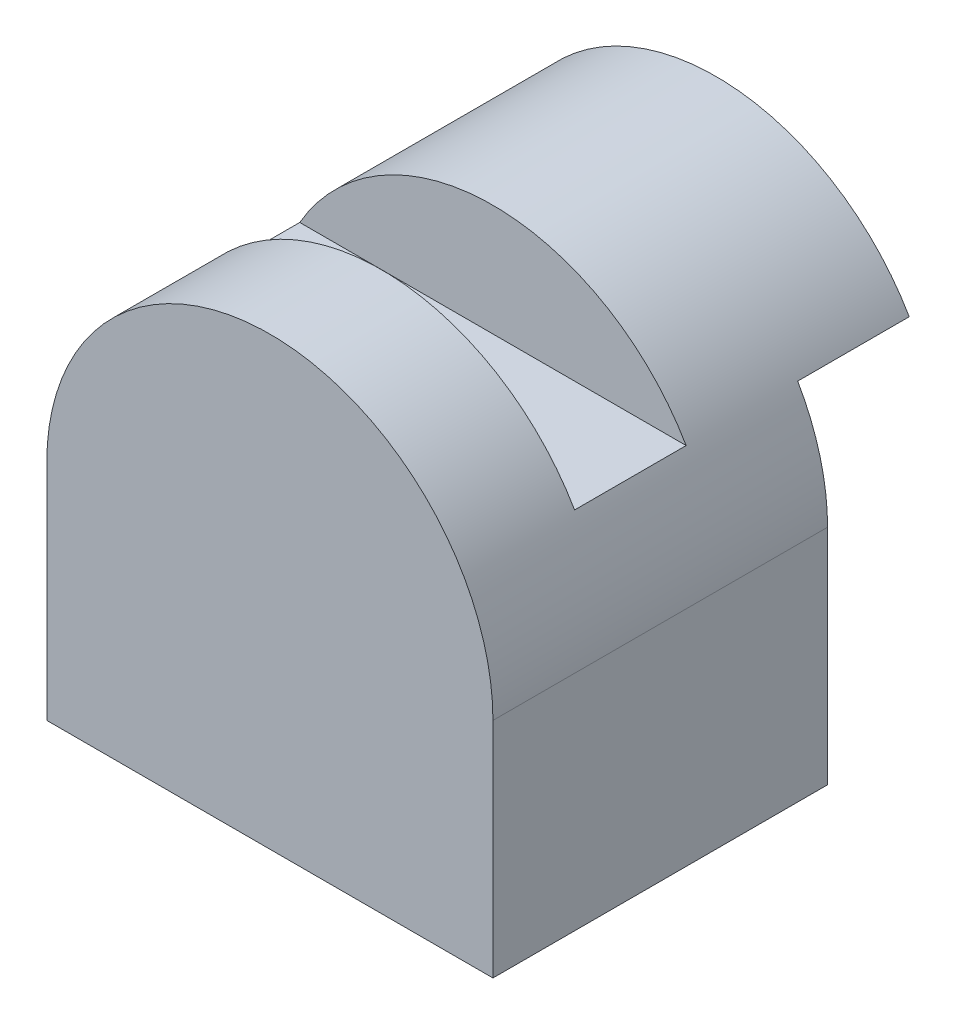
SolidWorks part; units mm, degrees
ref_plane "Front Plane" through (0, 0, 0) normal (0, 0, 1) x (1, 0, 0)
ref_plane "Top Plane" through (0, 0, 0) normal (0, 1, 0) x (1, 0, 0)
ref_plane "Right Plane" through (0, 0, 0) normal (1, 0, 0) x (0, 0, -1)
sketch "Sketch1" plane through (0, 0, 0) normal (0, 0, 1) x (1, 0, 0)
  line L0 (-20, 0) -> (-20, -20)
  line L1 (-20, -20) -> (20, -20)
  line L2 (20, -20) -> (20, 0)
  arc A0 (-20, 0) -> (20, 0) centre (0, 0) cw
  dimension "D1" = 20
  dimension "D2" = 20
  dimension "D3" = 20
extrude "Boss-Extrude1" add sketch "Sketch1" along normal blind 40
sketch "Sketch2" plane through (0, 0, 0) normal (1, 0, 0) x (0, 0, -1)
  line L0 (0, 20) -> (-40, 20) construction
  line L1 (0, -20) -> (-10, -20)
  line L2 (0, -20) -> (0, 10)
  line L3 (0, 10) -> (-10, 10)
  line L4 (-10, -20) -> (-10, 10)
  line L5 (-20, 20) -> (-30, 20)
  line L6 (-20, 20) -> (-20, 10)
  line L7 (-20, 10) -> (-30, 10)
  line L8 (-30, 20) -> (-30, 10)
  dimension "D1" = 30
  dimension "D2" = 10
  dimension "D3" = 10
  dimension "D4" = 10
  dimension "D5" = 10
extrude "Cut-Extrude1" cut sketch "Sketch2" against normal blind 40 and the other way blind 40
